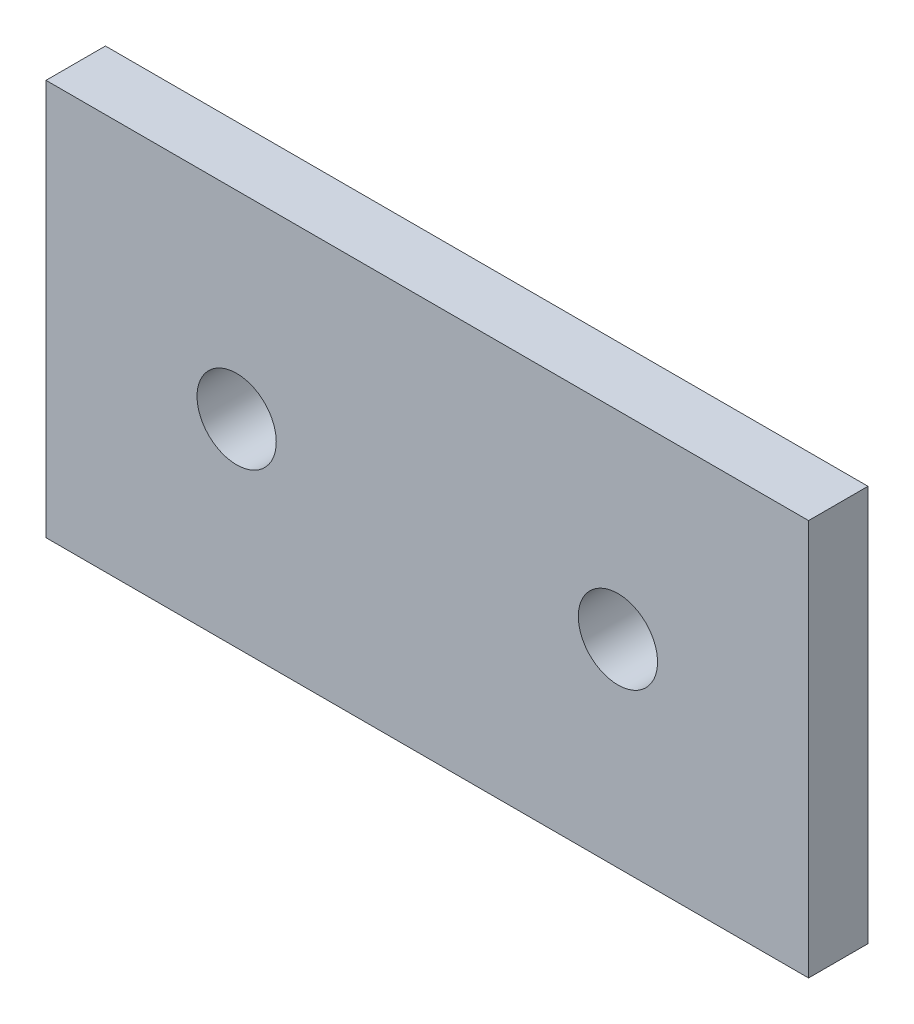
SolidWorks part; units mm, degrees
ref_plane "Alzado" through (0, 0, 0) normal (0, 0, 1) x (1, 0, 0)
ref_plane "Planta" through (0, 0, 0) normal (0, 1, 0) x (1, 0, 0)
ref_plane "Vista lateral" through (0, 0, 0) normal (1, 0, 0) x (0, 0, -1)
sketch "Croquis1" plane through (0, 0, 0) normal (0, 0, 1) x (1, 0, 0)
  line L0 (-19.25, 20) -> (-19.25, 0) construction
  line L1 (0, 0) -> (-38.5, 0)
  line L2 (0, 0) -> (0, 20)
  line L3 (0, 20) -> (-38.5, 20)
  line L4 (-38.5, 0) -> (-38.5, 20)
  dimension "D1" = 38.5
  dimension "D2" = 20
extrude "Saliente-Extruir1" add sketch "Croquis1" along normal blind 3
sketch "Croquis2" plane through (0, 0, 3) normal (0, 0, 1) x (1, 0, 0)
  line L0 (-19.25, 20) -> (-19.25, 0) construction
  line L1 (0, 20) -> (-38.5, 20) construction
  line L2 (-38.5, 0) -> (0, 0) construction
sketch "Croquis3" plane through (0, 0, 0) normal (0, 0, -1) x (-1, 0, 0)
  line L0 (19.25, 20) -> (19.25, 0) construction
  line L1 (38.5, 0) -> (0, 0) construction
  line L2 (38.5, 10) -> (0, 10) construction
  line L3 (0, 0) -> (0, 20) construction
  circle A0 centre (9.625, 10) radius 2
  circle A1 centre (28.875, 10) radius 2
  point P10 (19.25, 10)
  dimension "D2" = 4
  dimension "D1" = 9.625
extrude "Cortar-Extruir1" cut sketch "Croquis3" against normal blind 3 contours A0 | A1
